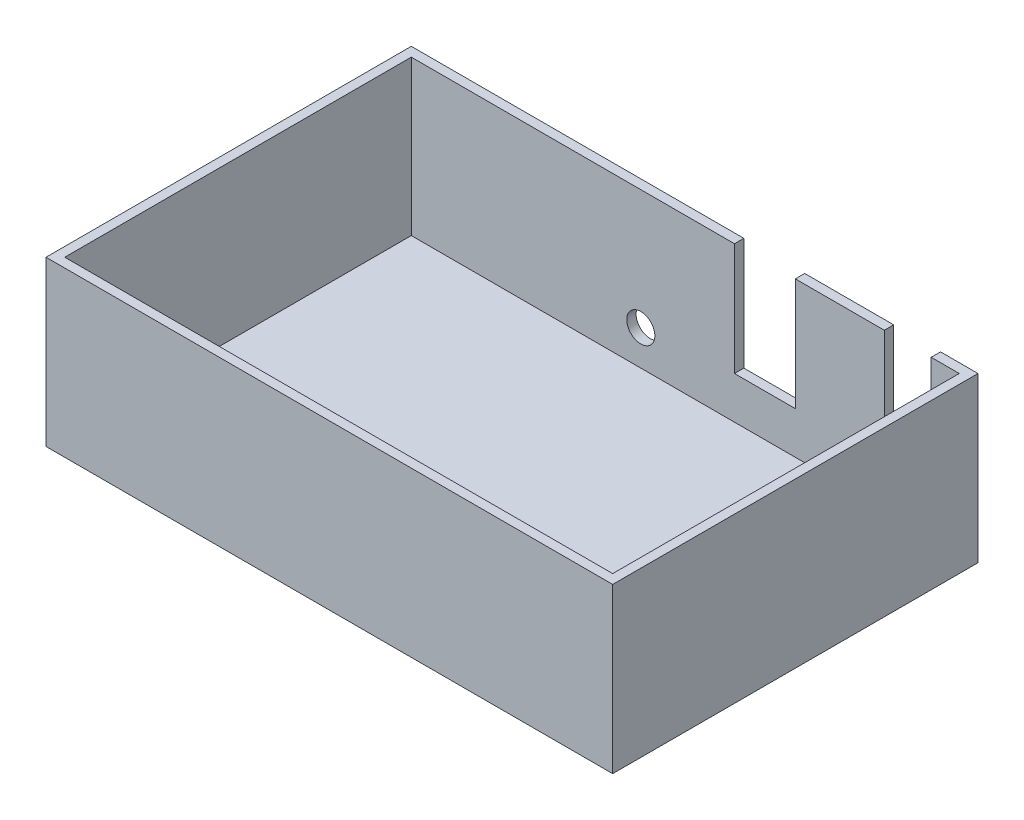
SolidWorks part; units mm, degrees
ref_plane "Front Plane" through (0, 0, 0) normal (0, 0, 1) x (1, 0, 0)
ref_plane "Top Plane" through (0, 0, 0) normal (0, 1, 0) x (1, 0, 0)
ref_plane "Right Plane" through (0, 0, 0) normal (1, 0, 0) x (0, 0, -1)
sketch "Sketch1" plane through (0, 0, 0) normal (0, 1, 0) x (1, 0, 0)
  line L1 (0, 0) -> (121, 0)
  line L2 (0, 0) -> (0, 78)
  line L3 (0, 78) -> (121, 78)
  line L4 (121, 0) -> (121, 78)
  line L5 (2, 76) -> (119, 76)
  line L6 (2, 76) -> (2, 2)
  line L7 (2, 2) -> (119, 2)
  line L8 (119, 76) -> (119, 2)
  dimension "D1" = 121
  dimension "D2" = 78
  dimension "D3" = 2
  dimension "D4" = 2
  dimension "D5" = 117
  dimension "D6" = 74
sketch "Sketch2" plane through (0, 0, 0) normal (0, 1, 0) x (1, 0, 0)
extrude "Boss-Extrude3" add sketch "Sketch1" along normal blind 35 contours L2 L1 L4 L3
sketch "Sketch4" plane through (0, 35, 0) normal (0, 1, 0) x (1, 0, 0)
  line L0 (0, -19.25) -> (0, 19.25) construction
  line L1 (119, 2) -> (2, 2)
  line L2 (119, 2) -> (119, 76)
  line L3 (119, 76) -> (2, 76)
  line L4 (2, 2) -> (2, 76)
  line L5 (0, 78) -> (121, 78) construction
  dimension "D1" = 117
  dimension "D2" = 74
  dimension "D3" = 2
  dimension "D4" = 2
extrude "Cut-Extrude1" cut sketch "Sketch4" against normal blind 33
sketch "Sketch5" plane through (0, 0, -78) normal (0, 0, -1) x (-1, 0, 0)
  line L0 (0, 35) -> (-121, 35) construction
  line L5 (-113, 35) -> (-103, 35)
  line L6 (-113, 35) -> (-113, 12)
  line L7 (-113, 12) -> (-103, 12)
  line L8 (-103, 35) -> (-103, 12)
  line L9 (-121, 35) -> (-121, 0) construction
  line L11 (-84, 35) -> (-71, 35)
  line L12 (-84, 35) -> (-84, 11)
  line L13 (-84, 11) -> (-71, 11)
  line L14 (-71, 35) -> (-71, 11)
  dimension "D1" = 23
  dimension "D2" = 8
  dimension "D3" = 10
  dimension "D4" = 24
  dimension "D5" = 13
  dimension "D6" = 19
extrude "Cut-Extrude2" cut sketch "Sketch5" against normal blind 33
sketch "Sketch6" plane through (0, 0, -78) normal (0, 0, -1) x (-1, 0, 0)
  line L0 (-121, 35) -> (-121, 0) construction
  circle A0 centre (-51, 9.4633) radius 3
  dimension "D1" = 70
  dimension "D2" = 6
extrude "Cut-Extrude3" cut sketch "Sketch6" against normal blind 33
sketch "Sketch7" plane through (0, 0, 0) normal (0, -1, 0) x (-1, 0, 0)
  text T0 "54"
extrude "Cut-Extrude4" cut sketch "Sketch7" against normal blind 1
